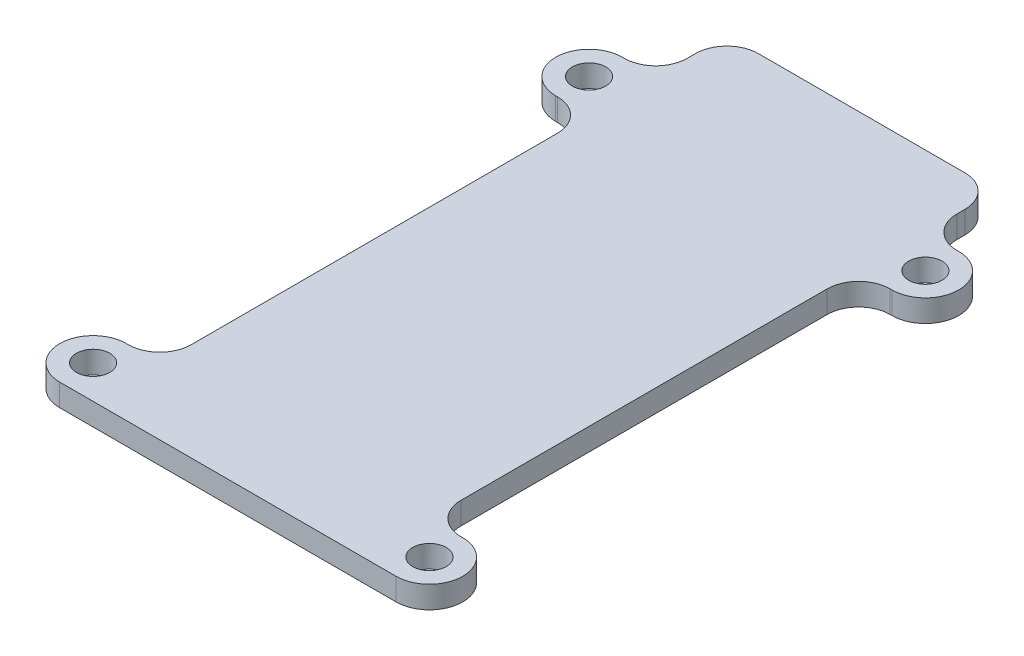
SolidWorks part; units mm, degrees
ref_plane "Front Plane" through (0, 0, 0) normal (0, 0, 1) x (1, 0, 0)
ref_plane "Top Plane" through (0, 0, 0) normal (0, 1, 0) x (1, 0, 0)
ref_plane "Right Plane" through (0, 0, 0) normal (1, 0, 0) x (0, 0, -1)
sketch "Sketch1" plane through (0, 0, 0) normal (0, 1, 0) x (1, 0, 0)
  line L0 (0, 132.63) -> (0, 28.05)
  line L1 (77, 169.68) -> (77, 172)
  line L2 (0, 172) -> (0, 169.68)
  line L3 (9, 181) -> (68, 181)
  line L4 (77, 28.05) -> (77, 132.63)
  line L5 (-9.525, 141.63) -> (-9, 141.63)
  line L6 (86, 160.68) -> (86.525, 160.68)
  line L7 (86.525, 141.63) -> (86, 141.63)
  line L8 (-9, 160.68) -> (-9.525, 160.68)
  line L10 (0, 0) -> (-9.525, 0)
  line L11 (86.525, 19.05) -> (86, 19.05)
  line L12 (77, 0) -> (86.525, 0)
  line L13 (-9.525, 19.05) -> (-9, 19.05)
  line L14 (0, 0) -> (77, 0)
  arc A0 (86.525, 141.63) -> (86.525, 160.68) centre (86.525, 151.155) ccw
  circle A1 centre (86.525, 151.155) radius 4.7625
  arc A2 (77, 132.63) -> (86, 141.63) centre (86, 132.63) cw
  arc A3 (0, 132.63) -> (-9, 141.63) centre (-9, 132.63) ccw
  circle A4 centre (-9.525, 151.155) radius 4.7625
  arc A5 (-9.525, 141.63) -> (-9.525, 160.68) centre (-9.525, 151.155) cw
  arc A6 (-9.525, 19.05) -> (-9.525, 0) centre (-9.525, 9.525) ccw
  circle A7 centre (-9.525, 9.525) radius 4.7625
  arc A8 (0, 28.05) -> (-9, 19.05) centre (-9, 28.05) cw
  arc A9 (77, 28.05) -> (86, 19.05) centre (86, 28.05) ccw
  circle A10 centre (86.525, 9.525) radius 4.7625
  arc A11 (86.525, 19.05) -> (86.525, 0) centre (86.525, 9.525) cw
  arc A12 (-9, 160.68) -> (0, 169.68) centre (-9, 169.68) ccw
  arc A13 (86, 160.68) -> (77, 169.68) centre (86, 169.68) cw
  arc A14 (68, 181) -> (77, 172) centre (68, 172) cw
  arc A15 (0, 172) -> (9, 181) centre (9, 172) cw
  dimension "D1" = 9
  dimension "D2" = 9
  dimension "D3" = 9
  dimension "D4" = 9
  dimension "D5" = 9
extrude "Boss-Extrude1" add sketch "Sketch1" along normal blind 6.35
